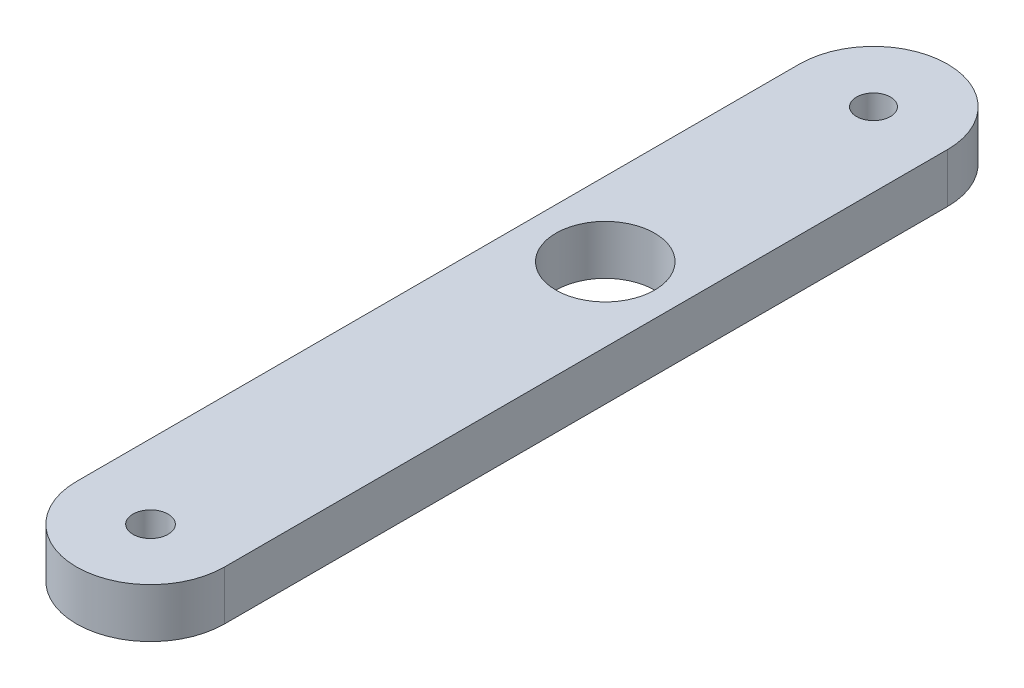
SolidWorks part; units mm, degrees
ref_plane "Front Plane" through (0, 0, 0) normal (0, 0, 1) x (1, 0, 0)
ref_plane "Top Plane" through (0, 0, 0) normal (0, 1, 0) x (1, 0, 0)
ref_plane "Right Plane" through (0, 0, 0) normal (1, 0, 0) x (0, 0, -1)
sketch "Sketch2" plane through (0, 0, 0) normal (0, 1, 0) x (1, 0, 0)
  line L1 (-6.7067, 20.0433) -> (-6.7067, -6.4567)
  line L2 (-16.2317, 20.0433) -> (-16.2317, -6.4567)
  line L6 (-16.2317, -26.4567) -> (-16.2317, -6.4567)
  line L7 (-6.7067, -26.4567) -> (-6.7067, -6.4567)
  arc A0 (-6.7067, 20.0433) -> (-16.2317, 20.0433) centre (-11.4692, 20.0433) ccw
  arc A1 (-16.2317, -26.4567) -> (-6.7067, -26.4567) centre (-11.4692, -26.4567) ccw
  circle A2 centre (-11.4692, 20.0433) radius 1.0922
  circle A4 centre (-11.4692, 2.7933) radius 3.175
  circle A7 centre (-11.4692, -26.4567) radius 1.1303
  point P2 (-11.4692, 2.7933)
  dimension "D3" = 17.25
  dimension "D1" = 4.7625
  dimension "D4" = 2.1844
  dimension "D5" = 6.35
  dimension "D6" = 20
  dimension "D8" = 2.2606
  dimension "D2" = 20
  dimension "D7" = 0
extrude "Boss-Extrude2" add sketch "Sketch2" along normal blind 3.175
